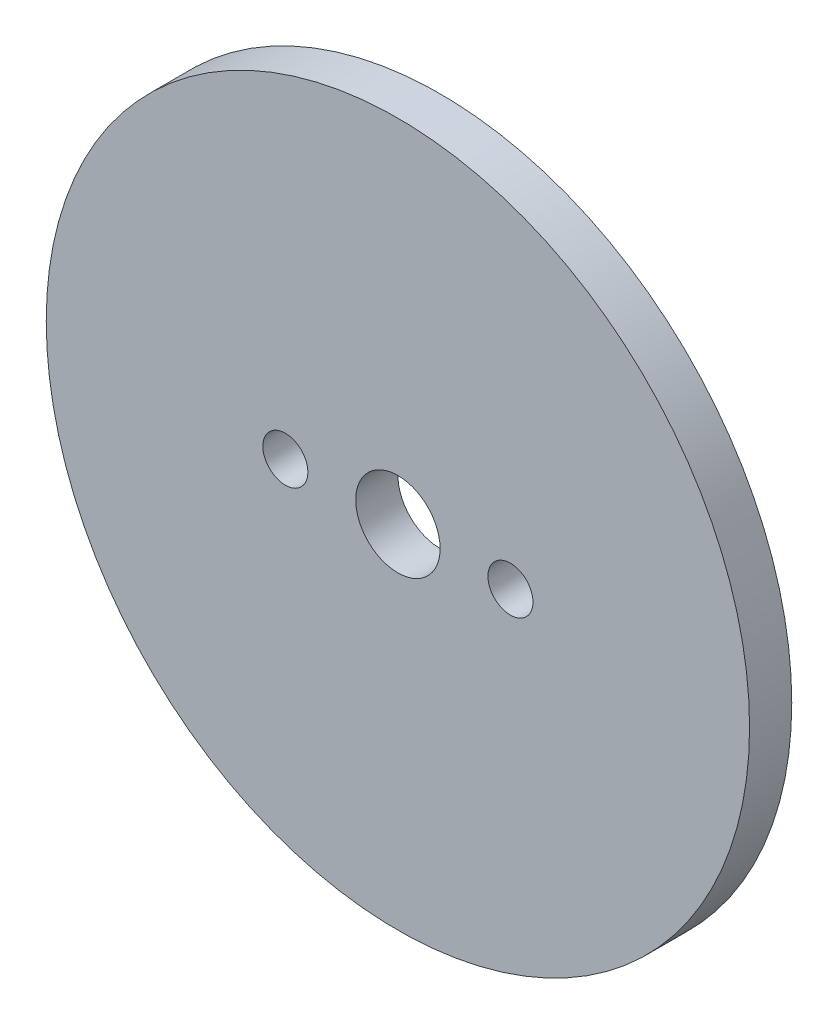
SolidWorks part; units mm, degrees
material "MDF"
ref_plane "Plano frontal" through (0, 0, 0) normal (0, 0, 1) x (1, 0, 0)
ref_plane "Plano superior" through (0, 0, 0) normal (0, 1, 0) x (1, 0, 0)
ref_plane "Plano direito" through (0, 0, 0) normal (1, 0, 0) x (0, 0, -1)
sketch "Esboço1" plane through (0, 0, 0) normal (0, 0, 1) x (1, 0, 0)
  line L0 (-8, 0) -> (8, 0) construction
  circle A0 centre (0, 0) radius 25
  circle A1 centre (0, 0) radius 3
  circle A2 centre (-8, 0) radius 1.6
  circle A3 centre (8, 0) radius 1.6
  dimension "D1" = 3.2
  dimension "D2" = 6
  dimension "D4" = 50
  dimension "D3" = 16
extrude "Ressalto-extrusão1" add sketch "Esboço1" along normal mid plane 3
